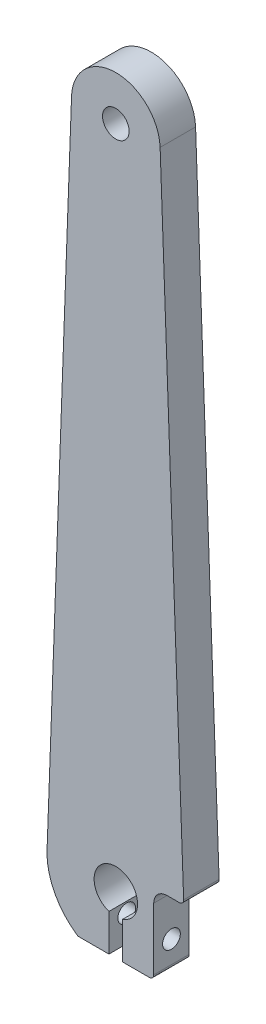
SolidWorks part; units mm, degrees
ref_plane "Front Plane" through (0, 0, 0) normal (0, 0, 1) x (1, 0, 0)
ref_plane "Top Plane" through (0, 0, 0) normal (0, 1, 0) x (1, 0, 0)
ref_plane "Right Plane" through (0, 0, 0) normal (1, 0, 0) x (0, 0, -1)
sketch "Sketch1" plane through (0, 0, 0) normal (0, 0, 1) x (1, 0, 0)
  line L1 (-16, -86.5) -> (16, -86.5)
  line L2 (-16, -86.5) -> (-16, 86.5)
  line L3 (-16, 86.5) -> (16, 86.5)
  line L4 (16, -86.5) -> (16, 86.5)
  line L5 (-16, -86.5) -> (16, 86.5) construction
  line L6 (-16, 86.5) -> (16, -86.5) construction
  point P0 (0, 0)
  dimension "D1" = 173
  dimension "D2" = 32
extrude "Boss-Extrude2" add sketch "Sketch1" along normal blind 8
sketch "Sketch3" plane through (0, 0, 8) normal (0, 0, 1) x (1, 0, 0)
  line L0 (-16, -86.5) -> (16, -86.5) construction
  line L1 (16, 86.5) -> (-16, 86.5) construction
  line L2 (0, -73.5) -> (0, -86.5) construction
  line L4 (-1.55, -86.5) -> (1.55, -86.5)
  line L5 (-1.55, -86.5) -> (-1.55, -78.15)
  line L6 (-1.55, -78.15) -> (1.55, -78.15)
  line L7 (1.55, -86.5) -> (1.55, -78.15)
  circle A0 centre (0, -73.5) radius 4.9
  circle A1 centre (0, 76.5) radius 3
  point P13 (0, -86.5)
  dimension "D2" = 9.8
  dimension "D3" = 6
  dimension "D1" = 13
  dimension "D4" = 10
  dimension "D5" = 3.1
  dimension "D6" = 8.35
extrude "Cut-Extrude1" cut sketch "Sketch3" against normal through all
sketch "Sketch4" plane through (0, 0, 8) normal (0, 0, 1) x (1, 0, 0)
  point P0 (0, 76.5)
  point P1 (0, -73.5)
sketch "Sketch5" plane through (0, 0, 8) normal (0, 0, 1) x (1, 0, 0)
  line L0 (-16, -86.5) -> (-15.541, -74.0298)
  line L2 (-16, -86.5) -> (16, -86.5)
  line L3 (16, 86.5) -> (-16, 86.5)
  line L4 (-16, 86.5) -> (-16, -86.5)
  line L5 (-15.46, -71.8291) -> (-10, 76.5)
  line L6 (8.55, -86.5) -> (8.55, -68.5)
  line L7 (8.55, -68.5) -> (15.3382, -68.5)
  line L9 (15.3382, -68.5) -> (9.9932, 76.8674)
  arc A0 (9.9932, 76.8674) -> (-10, 76.5) centre (0, 76.5) ccw
  arc A1 (-15.46, -71.8291) -> (-8.5324, -86.5) centre (0, -73.5) ccw
  dimension "D1" = 20
  dimension "D2" = 31.1
  dimension "D3" = 7
  dimension "D4" = 18
extrude "Cut-Extrude4" cut sketch "Sketch5" against normal through all
fillet "Fillet1" radius 1 1 edges at (8.55, -86.5, 4)
fillet "Fillet3" radius 1 1 edges at (15.3382, -68.5, 4)
fillet "Fillet5" radius 3 1 edges at (8.55, -68.5, 4)
fillet "Fillet6" radius 0.5 1 edges at (-8.5324, -86.5, 4)
sketch "Sketch7" plane through (8.55, 0, 0) normal (1, 0, 0) x (0, 0, -1)
  line L0 (-8, -85.5) -> (0, -85.5) construction
  circle A0 centre (-4, -80.5) radius 2
  point P0 (-4, -85.5)
  dimension "D1" = 4
  dimension "D2" = 5
extrude "Cut-Extrude5" cut sketch "Sketch7" against normal through all
ref_plane "Plane1" through (0, 0, 4) normal (0, 0, 1) x (1, 0, 0)
sketch "Sketch8" plane through (0, 0, 4) normal (0, 0, 1) x (1, 0, 0)
  point P0 (0, -73.5)
sketch "Sketch9" plane through (0, 0, 4) normal (0, 0, 1) x (1, 0, 0)
  line L0 (0, -73.5) -> (0, 76.5) construction
